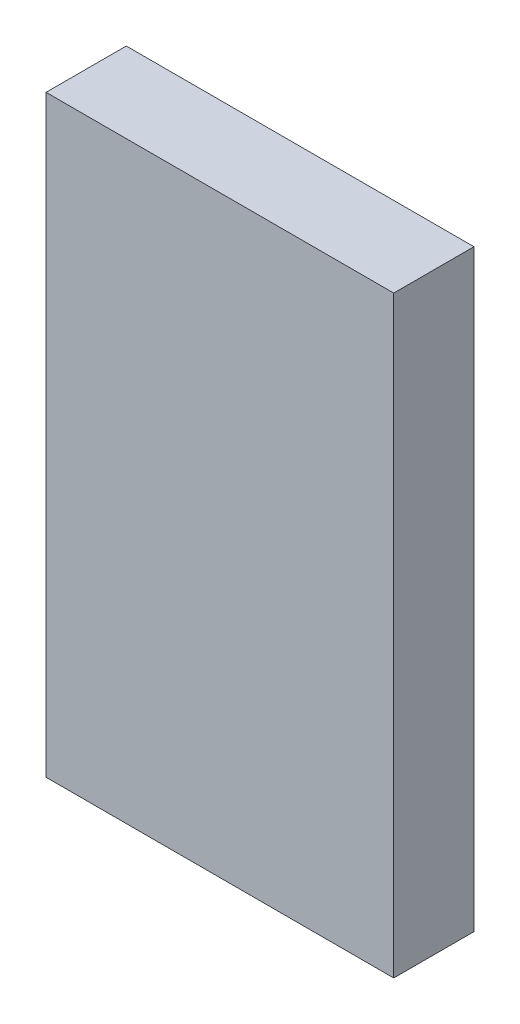
SolidWorks part; units mm, degrees
ref_plane "Front" through (0, 0, 0) normal (0, 0, 1) x (1, 0, 0)
ref_plane "Top" through (0, 0, 0) normal (0, 1, 0) x (1, 0, 0)
ref_plane "Right" through (0, 0, 0) normal (1, 0, 0) x (0, 0, -1)
sketch "草图1" plane through (0, 0, 0) normal (0, 0, 1) x (1, 0, 0)
  line L1 (0, 0) -> (2, 0)
  line L2 (0, 0) -> (0, -5)
  line L3 (0, -5) -> (2, -5)
  line L4 (2, 0) -> (2, -5)
  line L5 (2, -5) -> (7, -5)
  line L6 (2, -5) -> (2, -3)
  line L7 (2, -3) -> (7, -3)
  line L8 (7, -5) -> (7, -3)
  line L9 (7, -5) -> (5, -5)
  line L10 (7, -5) -> (7, -9)
  line L11 (7, -9) -> (5, -9)
  line L12 (5, -5) -> (5, -9)
  line L13 (5, -9) -> (0, -9)
  line L14 (5, -9) -> (5, -7)
  line L15 (5, -7) -> (0, -7)
  line L16 (0, -9) -> (0, -7)
  line L17 (0, -9) -> (2, -9)
  line L18 (0, -9) -> (0, -16.18)
  line L19 (0, -16.18) -> (2, -16.18)
  line L20 (2, -9) -> (2, -16.18)
  line L21 (-3, -19.18) -> (10, -19.18)
  line L22 (-3, -19.18) -> (-3, 3)
  line L23 (-3, 3) -> (10, 3)
  line L24 (10, -19.18) -> (10, 3)
  dimension "D1" = 2
  dimension "D2" = 5
  dimension "D3" = 2
  dimension "D4" = 2
  dimension "D5" = 2
  dimension "D6" = 4
  dimension "D7" = 5
  dimension "D8" = 5
  dimension "D9" = 7.18
  dimension "D10" = 3
  dimension "D11" = 3
  dimension "D12" = 3
  dimension "D13" = 3
extrude "凸台-拉伸1" add sketch "草图1" against normal blind 2 contours L21 L24 L23 L22 L13 L20 L19 L18 L16 L15 L12 L5 L3 L2 L1 L4 L7 L8 L10 L11
sketch "草图2" plane through (0, 0, 0) normal (0, 0, 1) x (1, 0, 0)
  line L1 (10, 3) -> (-3, 3)
  line L2 (10, 3) -> (10, -19.18)
  line L3 (10, -19.18) -> (-3, -19.18)
  line L4 (-3, 3) -> (-3, -19.18)
extrude "凸台-拉伸3" add sketch "草图2" along normal blind 1
sketch "草图3" plane through (0, 0, 0) normal (1, 0, 0) x (0, 0, -1)
  line L0 (0, -16.18) -> (1.7321, -17.18)
  line L1 (0, -7) -> (0, -16.18) construction
  line L3 (2, -15.0253) -> (3.2369, -15.7394)
  line L4 (2, -16.18) -> (2, -15.0253)
  line L6 (2, -16.18) -> (0, -16.18)
  line L7 (2, -15.0253) -> (0, -16.18)
  dimension "D1" = 120
  dimension "D2" = 2
  dimension "D3" = 2
